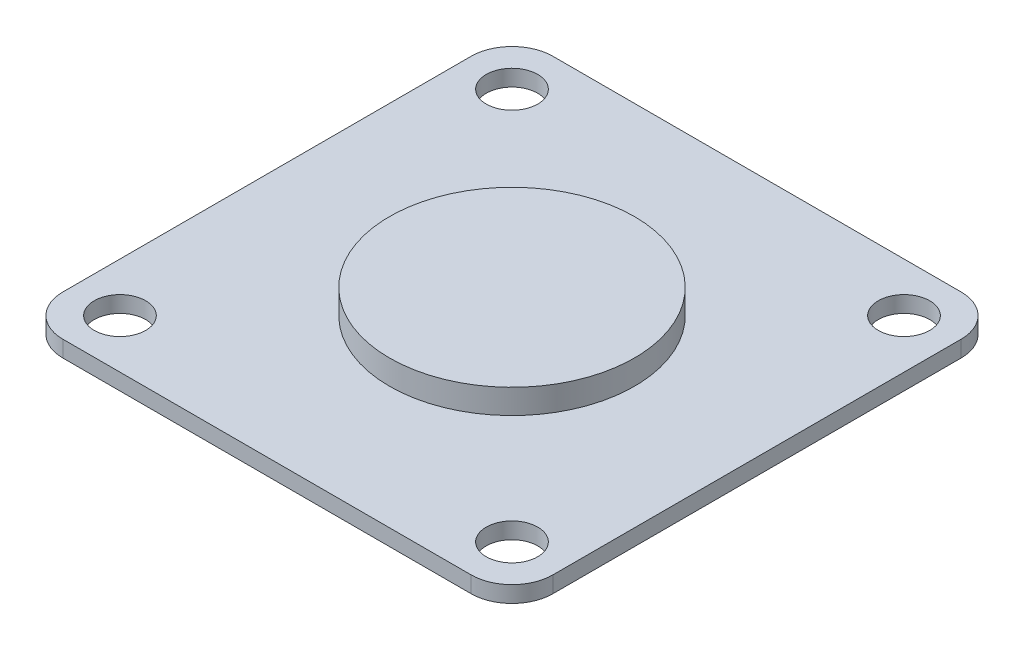
SolidWorks part; units mm, degrees
ref_plane "Plan de face" through (0, 0, 0) normal (0, 0, 1) x (1, 0, 0)
ref_plane "Plan de dessus" through (0, 0, 0) normal (0, 1, 0) x (1, 0, 0)
ref_plane "Plan de droite" through (0, 0, 0) normal (1, 0, 0) x (0, 0, -1)
sketch "Esquisse1" plane through (0, 0, 0) normal (0, 1, 0) x (1, 0, 0)
  line L0 (-24, 24) -> (-24, -24) construction
  line L1 (-25, -30) -> (25, -30)
  line L2 (-30, -25) -> (-30, 25)
  line L3 (-25, 30) -> (25, 30)
  line L4 (30, -25) -> (30, 25)
  line L5 (-30, -30) -> (30, 30) construction
  line L6 (-30, 30) -> (30, -30) construction
  line L7 (-24, 24) -> (24, 24) construction
  line L8 (24, 24) -> (24, -24) construction
  line L9 (24, -24) -> (-24, -24) construction
  circle A0 centre (-24, 24) radius 3.15
  circle A1 centre (24, 24) radius 3.15
  circle A2 centre (24, -24) radius 3.15
  circle A3 centre (-24, -24) radius 3.15
  arc A4 (25, 30) -> (30, 25) centre (25, 25) cw
  arc A5 (30, -25) -> (25, -30) centre (25, -25) cw
  arc A6 (-25, -30) -> (-30, -25) centre (-25, -25) cw
  arc A7 (-30, 25) -> (-25, 30) centre (-25, 25) cw
  point P0 (0, 0)
  point P11 (0, 0)
  point P14 (0, 0)
  point P17 (0, 0)
  point P20 (0, 0)
  dimension "D3" = 6.3
  dimension "D6" = 5
  dimension "D1" = 60
  dimension "D2" = 60
  dimension "D4" = 24
  dimension "D5" = 4
extrude "Boss.-Extru.1" add sketch "Esquisse1" along normal blind 2
sketch "Esquisse2" plane through (0, 2, 0) normal (0, 1, 0) x (1, 0, 0)
  circle A0 centre (0, 0) radius 15
  dimension "D1" = 30
extrude "Boss.-Extru.2" add sketch "Esquisse2" along normal blind 3
